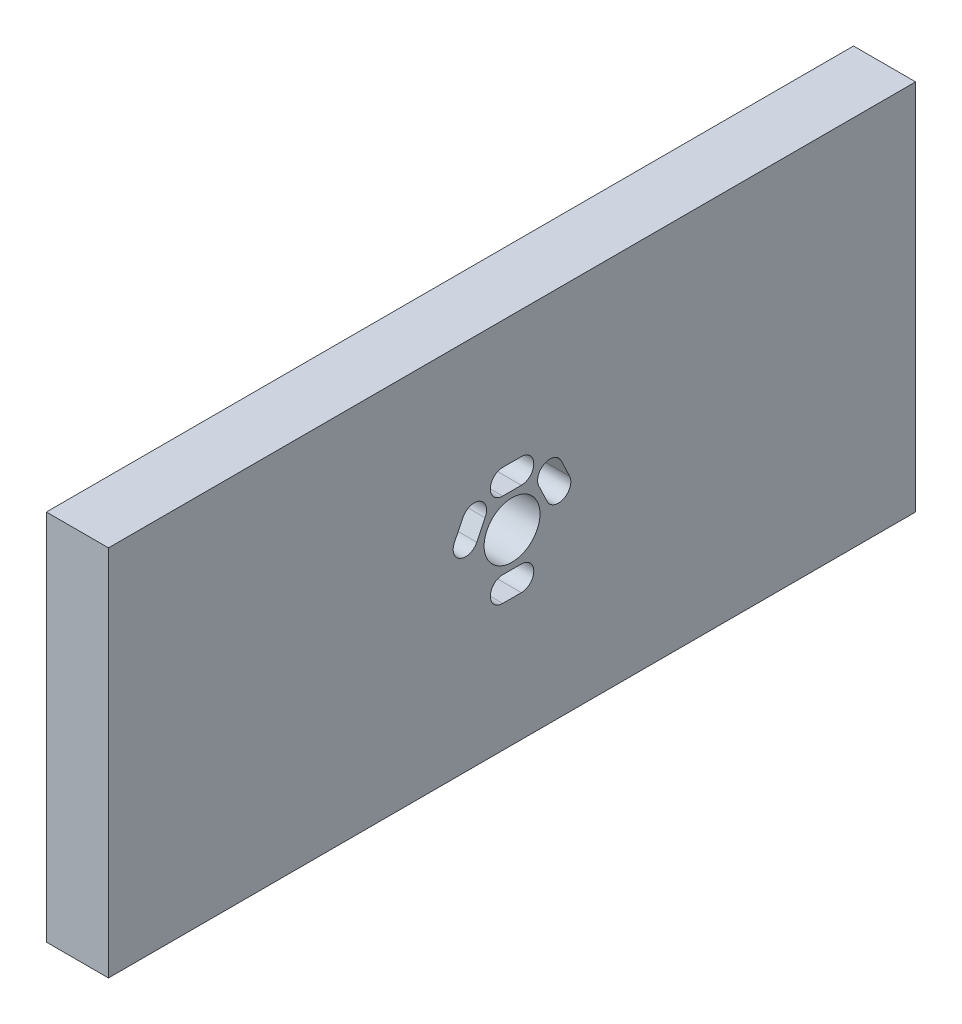
SolidWorks part; units mm, degrees
ref_plane "Front Plane" through (0, 0, 0) normal (0, 0, 1) x (1, 0, 0)
ref_plane "Top Plane" through (0, 0, 0) normal (0, 1, 0) x (1, 0, 0)
ref_plane "Right Plane" through (0, 0, 0) normal (1, 0, 0) x (0, 0, -1)
sketch "Sketch1" plane through (0, 0, 0) normal (1, 0, 0) x (0, 0, -1)
  line L9 (-61.1868, 57.8975) -> (68.8132, 57.8975)
  line L10 (-61.1868, 57.8975) -> (-61.1868, -2.1025)
  line L11 (-61.1868, -2.1025) -> (68.8132, -2.1025)
  line L12 (68.8132, 57.8975) -> (68.8132, -2.1025)
  line B0 (-5.4644, 30.7753) -> (-4.0816, 33.6063)
  line B1 (5.3132, 18.3975) -> (2.3132, 18.3975)
  line B2 (-0.5284, 31.7706) -> (-1.8696, 29.0208)
  line B3 (2.3132, 22.3975) -> (5.3132, 22.3975)
  line B4 (5.3132, 33.3742) -> (2.3132, 33.3742)
  line B5 (9.472, 29.0382) -> (8.081, 31.9616)
  line B6 (2.3132, 37.3742) -> (5.3132, 37.3742)
  line B7 (11.7336, 33.5893) -> (13.0834, 30.7583)
  circle B8 centre (3.8132, 27.8975) radius 4.5
  arc B9 (9.472, 29.0382) -> (13.0834, 30.7583) centre (11.2777, 29.8983) ccw
  arc B10 (11.7336, 33.5893) -> (8.081, 31.9616) centre (9.9281, 32.729) ccw
  arc B11 (-5.4644, 30.7753) -> (-1.8696, 29.0208) centre (-3.6672, 29.8975) ccw
  arc B12 (-0.5284, 31.7706) -> (-4.0816, 33.6063) centre (-2.2872, 32.7228) ccw
  arc B13 (2.3132, 37.3742) -> (2.3132, 33.3742) centre (2.3132, 35.3742) ccw
  arc B14 (5.3132, 33.3742) -> (5.3132, 37.3742) centre (5.3132, 35.3742) ccw
  arc B15 (2.3132, 22.3975) -> (2.3132, 18.3975) centre (2.3132, 20.3975) ccw
  arc B16 (5.3132, 18.3975) -> (5.3132, 22.3975) centre (5.3132, 20.3975) ccw
  dimension "D1" = 130
  dimension "D2" = 60
  dimension "D3" = 30
  dimension "D4" = 65
sketch_block_instance "Block1-1"
sketch_block "Block1"
extrude "Boss-Extrude1" add sketch "Sketch1" along normal blind 10
